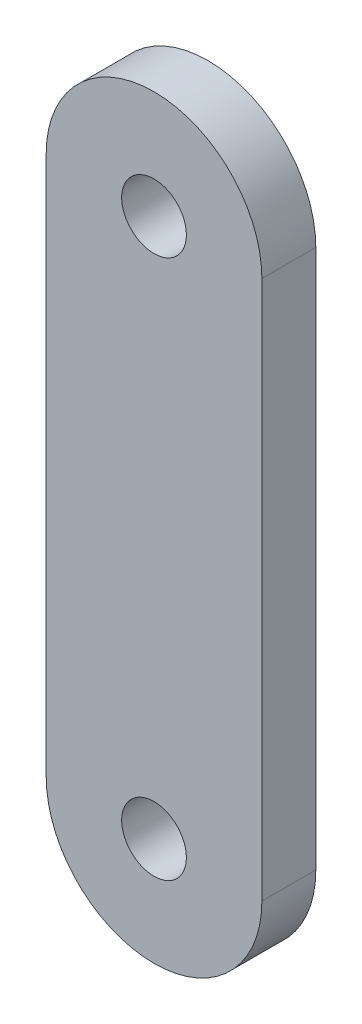
SolidWorks part; units mm, degrees
ref_plane "Alzado" through (0, 0, 0) normal (0, 0, 1) x (1, 0, 0)
ref_plane "Planta" through (0, 0, 0) normal (0, 1, 0) x (1, 0, 0)
ref_plane "Vista lateral" through (0, 0, 0) normal (1, 0, 0) x (0, 0, -1)
sketch "Croquis1" plane through (0, 0, 0) normal (0, 0, 1) x (1, 0, 0)
  line L0 (0, 0) -> (0, 25) construction
  line L1 (-5, 25) -> (-5, 0)
  line L2 (5, 0) -> (5, 25)
  circle A0 centre (0, 0) radius 1.5
  circle A1 centre (0, 25) radius 1.5
  arc A2 (5, 25) -> (-5, 25) centre (0, 25) ccw
  arc A3 (-5, 0) -> (5, 0) centre (0, 0) ccw
  dimension "D1" = 25
extrude "Saliente-Extruir1" add sketch "Croquis1" along normal blind 2.5
